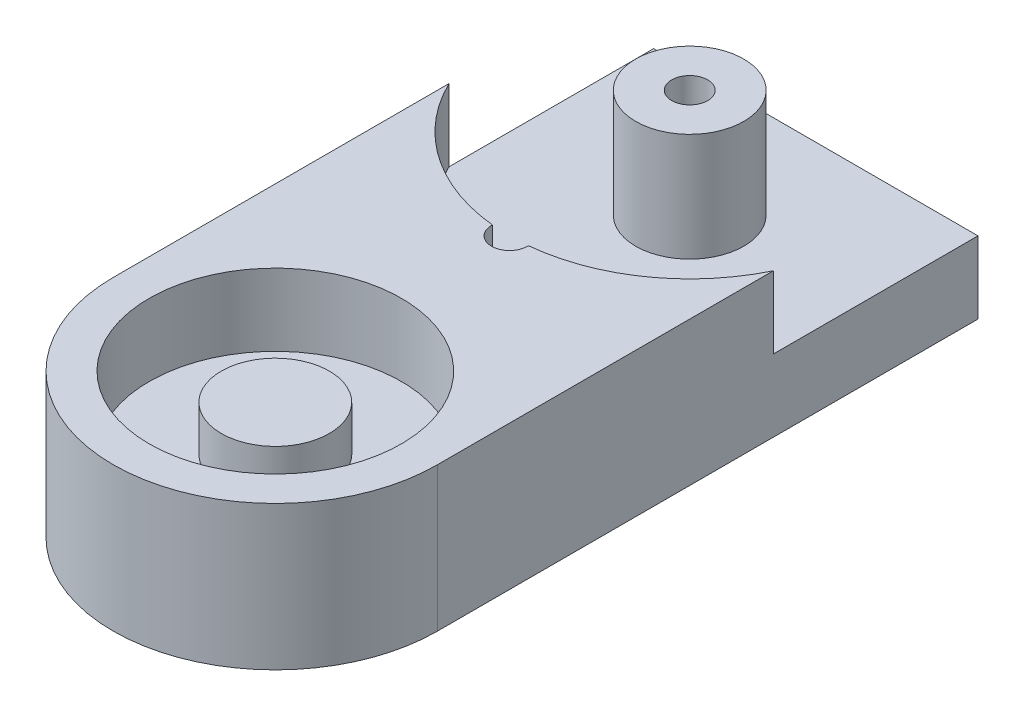
SolidWorks part; units mm, degrees
ref_plane "Front Plane" through (0, 0, 0) normal (0, 0, 1) x (1, 0, 0)
ref_plane "Top Plane" through (0, 0, 0) normal (0, 1, 0) x (1, 0, 0)
ref_plane "Right Plane" through (0, 0, 0) normal (1, 0, 0) x (0, 0, -1)
sketch "Sketch1" plane through (0, 0, 0) normal (0, 1, 0) x (1, 0, 0)
  line L0 (-3, 53.5049) -> (15, 53.5049)
  line L2 (-3, 23.5049) -> (-3, 53.5049)
  line L4 (15, 23.5049) -> (15, 53.5049)
  arc A0 (-3, 23.5049) -> (15, 23.5049) centre (6, 23.5049) ccw
  circle A1 centre (6, 36.5049) radius 1
  circle A2 centre (6, 46.5049) radius 1
extrude "Boss-Extrude1" add sketch "Sketch1" along normal blind 8
sketch "Sketch2" plane through (0, 8, 0) normal (0, 1, 0) x (1, 0, 0)
  circle A0 centre (6, 23.5049) radius 7
  circle A1 centre (6, 23.5049) radius 3
extrude "Cut-Extrude1" cut sketch "Sketch2" against normal blind 4
sketch "Sketch3" plane through (0, 8, 0) normal (0, 1, 0) x (1, 0, 0)
  circle A0 centre (6, 23.5049) radius 3
extrude "Cut-Extrude2" cut sketch "Sketch3" against normal blind 1.5
sketch "Sketch4" plane through (0, 8, 0) normal (0, 1, 0) x (1, 0, 0)
  line L2 (-4, 46.5049) -> (-4, 53.9936)
  line L3 (-4, 53.9936) -> (16, 53.9936)
  line L4 (16, 46.5049) -> (16, 53.9936)
  arc A0 (-4, 46.5049) -> (16, 46.5049) centre (6, 46.5049) ccw
extrude "Cut-Extrude3" cut sketch "Sketch4" against normal blind 4
sketch "Sketch5" plane through (15, 0, 0) normal (1, 0, 0) x (0, 0, -1)
  line L0 (23.5049, 8) -> (23.5049, 0) construction
  line L1 (53.5049, 0) -> (23.5049, 0)
  line L2 (53.5049, 0) -> (53.5049, 2)
  line L3 (53.5049, 2) -> (23.5049, 2)
  line L4 (23.5049, 0) -> (23.5049, 2)
  point P7 (53.5049, 1)
extrude "Boss-Extrude2" add sketch "Sketch5" against normal through all
sketch "Sketch6" plane through (0, 4, 0) normal (0, 1, 0) x (1, 0, 0)
  circle A0 centre (6, 46.5049) radius 3
  circle A1 centre (6, 46.5049) radius 1
extrude "Boss-Extrude3" add sketch "Sketch6" along normal blind 6
sketch "Sketch7" plane through (0, 0, -53.5049) normal (0, 0, -1) x (-1, 0, 0)
  circle A0 centre (-12, 2) radius 1
  circle A1 centre (0, 2) radius 1
extrude "Cut-Extrude4" cut sketch "Sketch7" against normal blind 5
